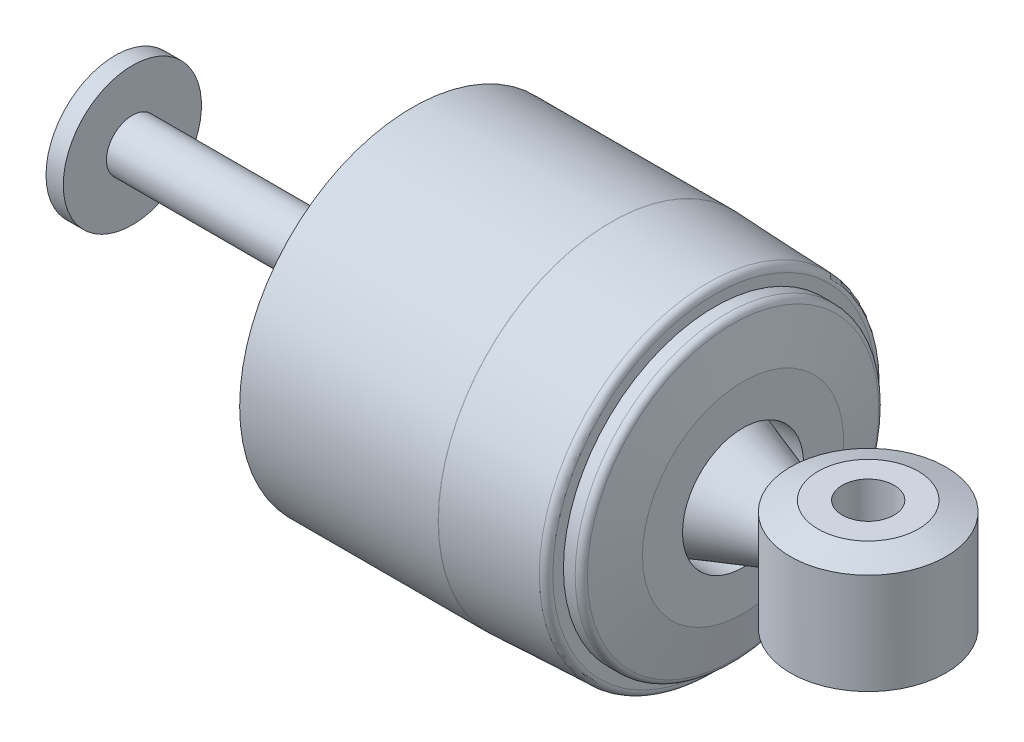
SolidWorks part; units mm, degrees
ref_plane "Front Plane" through (0, 0, 0) normal (0, 0, 1) x (1, 0, 0)
ref_plane "Top Plane" through (0, 0, 0) normal (0, 1, 0) x (1, 0, 0)
ref_plane "Right Plane" through (0, 0, 0) normal (1, 0, 0) x (0, 0, -1)
sketch "Sketch1" plane through (0, 0, 0) normal (0, 1, 0) x (1, 0, 0)
  line L0 (-68.0073, -5.1858) -> (-68.0073, 20.2142)
  line L1 (-68.0073, 20.2142) -> (-64.8323, 20.2142)
  line L2 (-64.8323, 20.2142) -> (-64.8323, 12.2767)
  line L3 (-64.8323, 12.2767) -> (41.8477, 12.2767)
  line L4 (41.8477, 12.2767) -> (41.8477, 18.6267)
  line L5 (41.8477, 18.6267) -> (57.8497, 13.2292)
  line L6 (57.8497, 13.2292) -> (57.8497, 1.7992)
  line L7 (-68.0073, 7.5142) -> (57.8497, 7.5142) construction
  line L8 (41.8477, -3.5983) -> (57.8497, 1.7992)
  line L9 (41.8477, 2.7517) -> (41.8477, -3.5983)
  line L10 (-64.8323, 2.7517) -> (41.8477, 2.7517)
  line L11 (-64.8323, -5.1858) -> (-64.8323, 2.7517)
  line L12 (-68.0073, -5.1858) -> (-64.8323, -5.1858)
  dimension "D1" = 3.175
  dimension "D2" = 106.68
  dimension "D3" = 25.4
  dimension "D4" = 9.525
  dimension "D5" = 11.43
  dimension "D6" = 6.35
  dimension "D7" = 16.002
revolve "Revolve1" add sketch "Sketch1" angle 360 about L7
sketch "Sketch2" plane through (0, 0, 0) normal (0, 1, 0) x (1, 0, 0)
  line L0 (70.4227, 7.5142) -> (57.8497, 7.5142) construction
  line L1 (57.8497, 1.7992) -> (57.8497, 13.2292) construction
  line L2 (41.8477, 18.6267) -> (41.8477, -3.5983) construction
  circle A0 centre (70.4227, 7.5142) radius 14.2875
  circle A1 centre (70.4227, 7.5142) radius 4.7625
  dimension "D1" = 9.525
  dimension "D2" = 28.575
  dimension "D3" = 28.575
extrude "Boss-Extrude1" add sketch "Sketch2" along normal mid plane 22.225 separate body
chamfer "Chamfer1" distance 5.08 angle 20 1 edges at (70.4227, 11.1125, 6.7733)
sketch "Sketch3" plane through (0, 0, 0) normal (0, 1, 0) x (1, 0, 0)
  line L0 (41.8477, 12.2767) -> (41.8477, 18.6267)
  line L1 (41.8477, 18.6267) -> (47.404, 18.6267)
  line L2 (47.404, 18.6267) -> (47.404, 25.9927)
  line L3 (47.404, 25.9927) -> (45.3584, 35.2955)
  line L4 (45.3584, 35.2955) -> (42.1834, 35.2955)
  line L5 (42.1834, 35.2955) -> (42.1834, 38.4705)
  line L6 (42.1834, 38.4705) -> (23.1499, 39.2642)
  line L7 (23.1499, 39.2642) -> (-13.3626, 39.2642)
  line L8 (-13.3626, 39.2642) -> (-13.3626, 38.4705)
  line L9 (-13.3626, 38.4705) -> (23.1334, 38.4705)
  line L10 (23.1334, 38.4705) -> (39.6434, 37.782)
  line L11 (39.6434, 37.782) -> (41.054, 27.7782)
  line L12 (41.054, 27.7782) -> (41.054, 12.2767)
  line L13 (41.8477, 12.2767) -> (-64.8323, 12.2767) construction
  line L14 (41.054, 12.2767) -> (41.8477, 12.2767)
  line L15 (-68.0867, 7.5142) -> (70.4227, 7.5142) construction
  line L16 (-64.8323, 7.5142) -> (-68.0073, 7.5142) construction
  line L17 (41.054, 2.7517) -> (41.8477, 2.7517)
  line L18 (41.054, -12.7497) -> (41.054, 2.7517)
  line L19 (39.6434, -22.7535) -> (41.054, -12.7497)
  line L20 (23.1334, -23.442) -> (39.6434, -22.7535)
  line L21 (-13.3626, -23.442) -> (23.1334, -23.442)
  line L22 (-13.3626, -24.2358) -> (-13.3626, -23.442)
  line L23 (23.1499, -24.2358) -> (-13.3626, -24.2358)
  line L24 (42.1834, -23.442) -> (23.1499, -24.2358)
  line L25 (42.1834, -20.267) -> (42.1834, -23.442)
  line L26 (45.3584, -20.267) -> (42.1834, -20.267)
  line L27 (47.404, -10.9643) -> (45.3584, -20.267)
  line L28 (47.404, -3.5983) -> (47.404, -10.9643)
  line L29 (41.8477, -3.5983) -> (47.404, -3.5983)
  line L30 (41.8477, 2.7517) -> (41.8477, -3.5983)
  dimension "D1" = 0.7937
  dimension "D2" = 63.5
  dimension "D3" = 36.5125
  dimension "D4" = 19.05
  dimension "D5" = 0.7937
  dimension "D6" = 6.35
  dimension "D7" = 0.7937
  dimension "D8" = 3.175
  dimension "D9" = 3.175
  dimension "D10" = 9.525
  dimension "D11" = 7.366
  dimension "D12" = 10.1027
  dimension "D13" = 2.54
revolve "Revolve2" add sketch "Sketch3" angle 360 about L15
fillet "Fillet1" radius 1.27 3 edges at (23.1499, 0, 24.2358) (42.1834, 0, 23.442) (45.3584, 0, 20.267)
